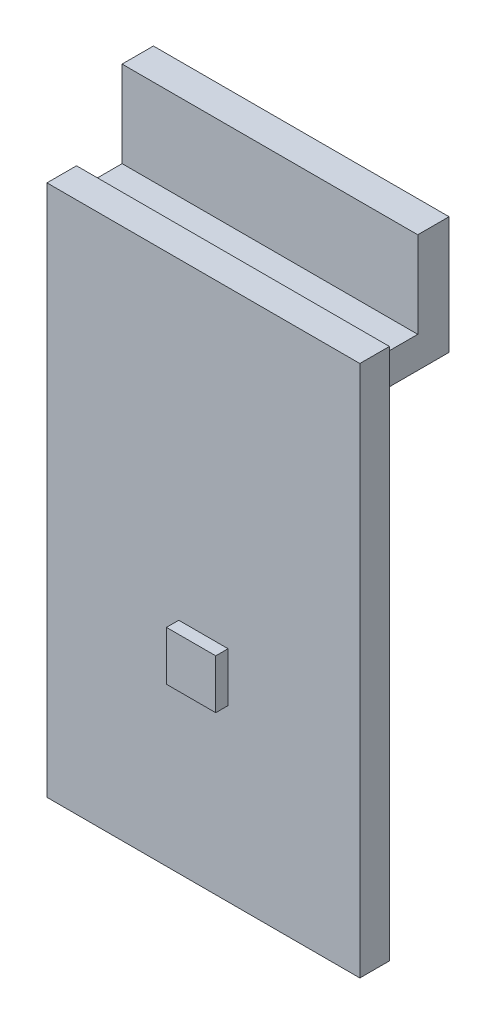
SolidWorks part; units mm, degrees
ref_plane "Plano frontal" through (0, 0, 0) normal (0, 0, 1) x (1, 0, 0)
ref_plane "Plano superior" through (0, 0, 0) normal (0, 1, 0) x (1, 0, 0)
ref_plane "Plano direito" through (0, 0, 0) normal (1, 0, 0) x (0, 0, -1)
sketch "Esboço1" plane through (0, 0, 0) normal (0, 0, 1) x (1, 0, 0)
  line L1 (-6.35, 10.8) -> (6.35, 10.8)
  line L2 (-6.35, 10.8) -> (-6.35, -10.8)
  line L3 (-6.35, -10.8) -> (6.35, -10.8)
  line L4 (6.35, 10.8) -> (6.35, -10.8)
  line L5 (-6.35, 10.8) -> (6.35, -10.8) construction
  line L6 (-6.35, -10.8) -> (6.35, 10.8) construction
  point P0 (0, 0)
  dimension "D1" = 21.6
  dimension "D2" = 12.7
extrude "Ressalto-extrusão1" add sketch "Esboço1" along normal blind 1.2
sketch "Esboço2" plane through (0, 0, 1.2) normal (0, 0, 1) x (1, 0, 0)
  line L0 (6.35, 10.8) -> (-6.35, 10.8) construction
  line L1 (-1, -1.9) -> (1, -1.9)
  line L2 (-1, -1.9) -> (-1, -3.9)
  line L3 (-1, -3.9) -> (1, -3.9)
  line L4 (1, -1.9) -> (1, -3.9)
  line L5 (-1, -1.9) -> (1, -3.9) construction
  line L6 (-1, -3.9) -> (1, -1.9) construction
  point P0 (0, -2.9)
  point P5 (0, 0)
  point P7 (0, 2.1177)
  dimension "D1" = 2
  dimension "D2" = 13.7
extrude "Ressalto-extrusão2" add sketch "Esboço2" along normal blind 0.5
sketch "Esboço3" plane through (0, 0, 0) normal (1, 0, 0) x (0, 0, -1)
  line L0 (0, 10.3) -> (1.5, 10.3)
  line L1 (0, 10.8) -> (0, -10.8) construction
  line L2 (1.5, 10.3) -> (1.5, 13.8)
  line L3 (1.5, 13.8) -> (2.77, 13.8)
  line L4 (2.77, 13.8) -> (2.77, 9.03)
  line L5 (2.77, 9.03) -> (0, 9.03)
  line L6 (0, 9.03) -> (0, 10.3)
  line L7 (-1.2, 10.8) -> (0, 10.8) construction
  dimension "D1" = 0.5
  dimension "D2" = 1.27
  dimension "D3" = 1.5
  dimension "D4" = 3.5
extrude "Ressalto-extrusão3" add sketch "Esboço3" along normal mid plane 12
